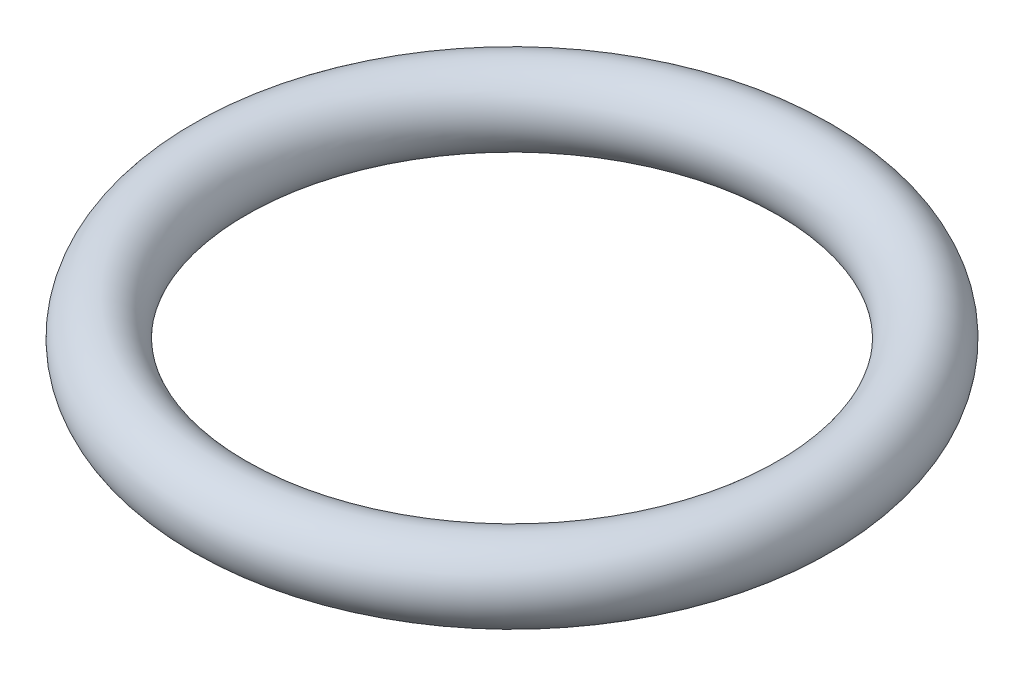
SolidWorks part; units mm, degrees
ref_plane "Plan de face" through (0, 0, 0) normal (0, 0, 1) x (1, 0, 0)
ref_plane "Plan de dessus" through (0, 0, 0) normal (0, 1, 0) x (1, 0, 0)
ref_plane "Plan de droite" through (0, 0, 0) normal (1, 0, 0) x (0, 0, -1)
sketch "Esquisse1" plane through (0, 0, 0) normal (0, 1, 0) x (1, 0, 0)
  circle A0 centre (0, 0) radius 11.75
  dimension "D1" = 23.5
sketch "Esquisse2" plane through (0, 0, 0) normal (1, 0, 0) x (0, 0, -1)
  line L0 (11.75, 0) -> (-11.75, 0) construction
  circle A0 centre (11.75, 0) radius 1.5
  dimension "D1" = 3
sweep "Balayage1" add profiles "Esquisse2" path "Esquisse1"
ref_point "Point1"
ref_plane "Plan1" through (0, 1.5, 0) normal (0, 1, 0) x (1, 0, 0)
